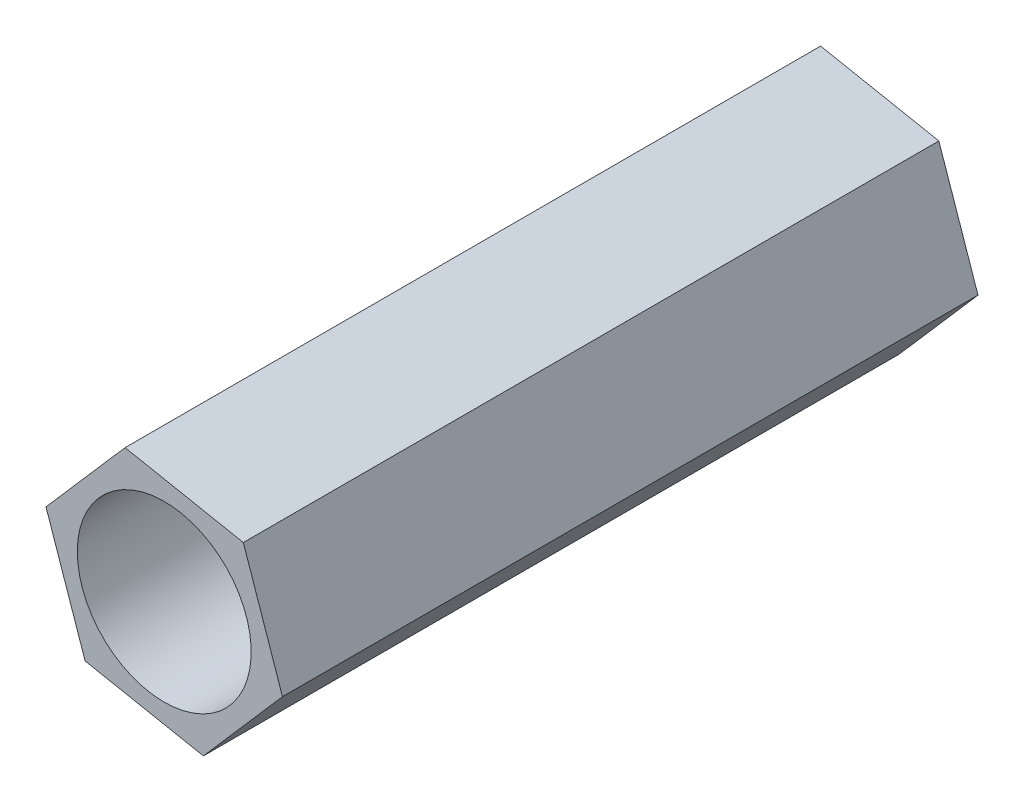
SolidWorks part; units mm, degrees
ref_plane "前视基准面" through (0, 0, 0) normal (0, 0, 1) x (1, 0, 0)
ref_plane "上视基准面" through (0, 0, 0) normal (0, 1, 0) x (1, 0, 0)
ref_plane "右视基准面" through (0, 0, 0) normal (1, 0, 0) x (0, 0, -1)
other "Configuration Table"
sketch "草图1" plane through (0, 0, 0) normal (0, 0, 1) x (1, 0, 0)
  line L1 (0.5628, -1.6381) -> (1.7, -0.3317)
  line L2 (1.7, -0.3317) -> (1.1372, 1.3064)
  line L3 (1.1372, 1.3064) -> (-0.5628, 1.6381)
  line L4 (-0.5628, 1.6381) -> (-1.7, 0.3317)
  line L5 (-1.7, 0.3317) -> (-1.1372, -1.3064)
  line L6 (-1.1372, -1.3064) -> (0.5628, -1.6381)
  circle A0 centre (0, 0) radius 1.5 construction
  dimension "D1" = 3
  dimension "D2" = 1.7
extrude "凸台-拉伸1" add sketch "草图1" against normal blind 10
hole_wizard "M3 螺纹孔1" positions "草图3" profile "草图4" tap size "M3" standard "GB" end condition through all
sketch "草图3" plane through (0, 0, -10) normal (0, 0, -1) x (-1, 0, 0)
  point P0 (0, 0)
sketch "草图4" plane through (0, 0, -10) normal (1, 0, 0) x (0, 1, 0)
  line L0 (0, 0) -> (0, 10)
  line L1 (0, 10) -> (1.25, 10)
  line L2 (1.25, 10) -> (1.25, 0)
  line L5 (1.25, 0) -> (0, 0)
  line L11 (0, -6.35) -> (0, 107.95) construction
  dimension "通孔螺纹孔钻头直径" = 2.5
  dimension "通孔螺纹孔钻头深度" = 10
cosmetic thread "孔螺蚊线1"
